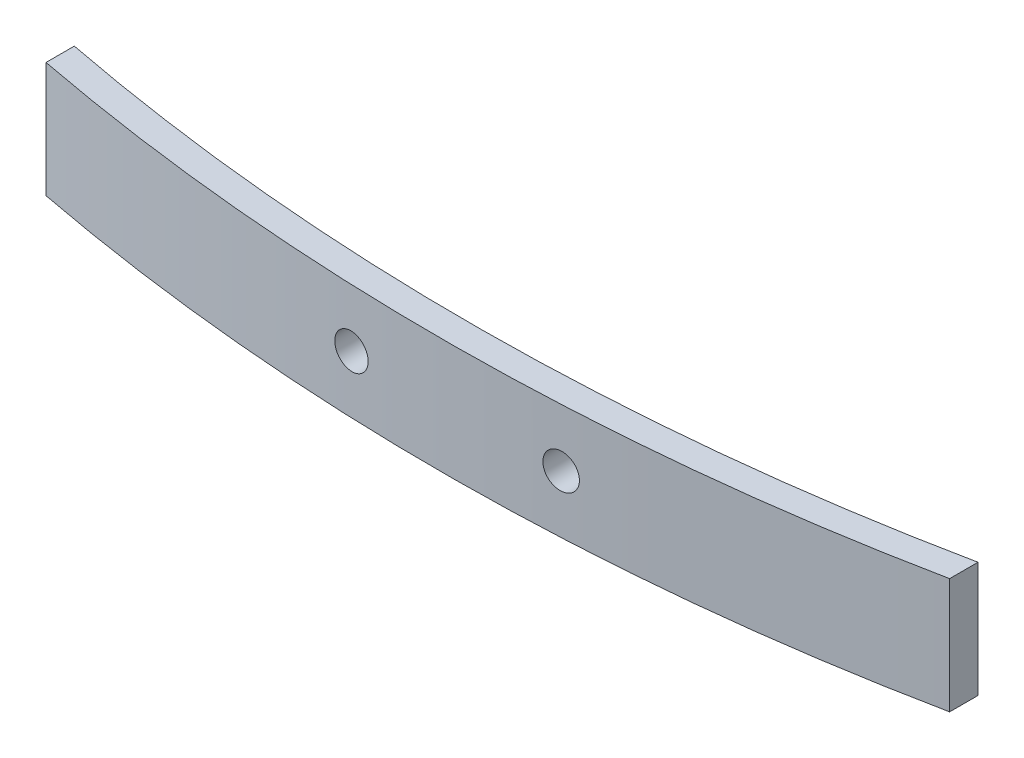
SolidWorks part; units mm, degrees
ref_plane "Front Plane" through (0, 0, 0) normal (0, 0, 1) x (1, 0, 0)
ref_plane "Top Plane" through (0, 0, 0) normal (0, 1, 0) x (1, 0, 0)
ref_plane "Right Plane" through (0, 0, 0) normal (1, 0, 0) x (0, 0, -1)
sketch "Sketch1" plane through (0, 0, 0) normal (0, 1, 0) x (1, 0, 0)
  line L0 (-35, 4.1426) -> (35, 4.5206) construction
  line L3 (-32.5, 11.9983) -> (-32.5, -12.2817) construction
  line L4 (32.5, 20.0549) -> (32.5, -12.2817) construction
  line L5 (-32.3092, 2.3199) -> (-32.3092, 0.2831)
  line L6 (32.3291, 2.6689) -> (32.3291, 0.6278)
  arc A4 (-32.3092, 2.3199) -> (32.3291, 2.6689) centre (-0.865, 164.5106) ccw
  arc A5 (-32.3092, 0.2831) -> (32.3291, 0.6278) centre (-0.865, 164.5106) ccw
  arc A7 (-35, 2.8648) -> (35, 3.2398) centre (-0.865, 164.5106) ccw construction
  arc A9 (-35.4132, 0.908) -> (35.4342, 1.2875) centre (-0.865, 164.5106) ccw construction
  point P4 (-35, 4.1426)
  point P7 (38.108, 5.4708)
  point P8 (35, 4.5206)
  point P18 (-31.892, 5.0928)
  dimension "D3" = 70
  dimension "D4" = 35
  dimension "D6" = 65
  dimension "D8" = 32.5
  dimension "D7" = 2
extrude "Boss-Extrude1" add sketch "Sketch1" along normal blind 8.3
sketch "Sketch2" plane through (0, 0, 0) normal (0, 0, 1) x (1, 0, 0)
  line L0 (0.0099, 8.3) -> (0, 0) construction
  line L1 (32.3291, 8.3) -> (-32.3092, 8.3) construction
  circle A0 centre (7.505, 4.15) radius 1.25
  circle A1 centre (-7.495, 4.15) radius 1.25
  point P15 (0.005, 4.15)
  dimension "D2" = 2.5
  dimension "D3" = 2.5
  dimension "D1" = 15
  dimension "D4" = 7.5
extrude "Cut-Extrude1" cut sketch "Sketch2" against normal through all both and the other way through all
